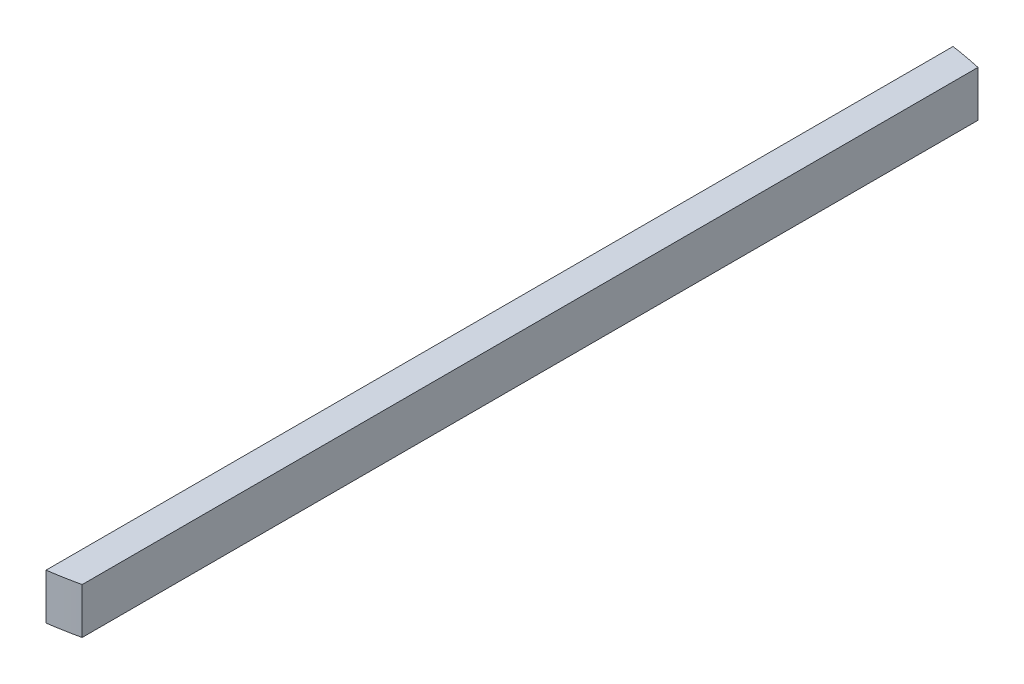
SolidWorks part; units mm, degrees
material "Polylactic Acid (PLA)"
ref_plane "Front Plane" through (0, 0, 0) normal (0, 0, 1) x (1, 0, 0)
ref_plane "Top Plane" through (0, 0, 0) normal (0, 1, 0) x (1, 0, 0)
ref_plane "Right Plane" through (0, 0, 0) normal (1, 0, 0) x (0, 0, -1)
sketch "Sketch2" plane through (0, 0, 0) normal (0, 1, 0) x (1, 0, 0)
  line L0 (3.81, 34.5009) -> (3.81, -47.4724) construction
  line L1 (10.16, -46.5286) -> (10.16, 46.5286)
  line L2 (6.985, 47.11) -> (6.985, -47.11)
  arc A0 (10.16, 46.5286) -> (6.985, 47.11) centre (0, 0) ccw
  arc A1 (6.985, -47.11) -> (10.16, -46.5286) centre (0, 0) ccw
  dimension "D3" = 95.25
  dimension "D1" = 6.35
  dimension "D2" = 3.175
  dimension "D4" = 3.81
extrude "Boss-Extrude1" add sketch "Sketch2" along normal blind 4.7625
